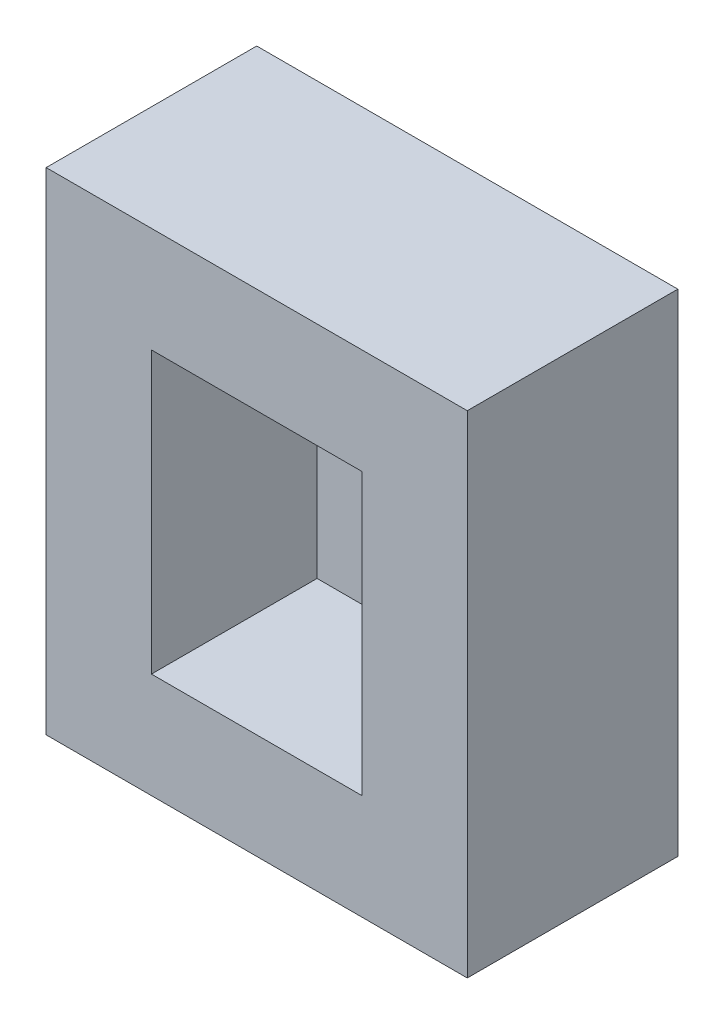
SolidWorks part; units mm, degrees
ref_plane "Front Plane" through (0, 0, 0) normal (0, 0, 1) x (1, 0, 0)
ref_plane "Top Plane" through (0, 0, 0) normal (0, 1, 0) x (1, 0, 0)
ref_plane "Right Plane" through (0, 0, 0) normal (1, 0, 0) x (0, 0, -1)
sketch "Sketch1" plane through (0, 0, 0) normal (0, 1, 0) x (1, 0, 0)
  line L1 (0, 0) -> (609.6, 0)
  line L2 (0, 0) -> (0, 304.8)
  line L3 (0, 304.8) -> (609.6, 304.8)
  line L4 (609.6, 0) -> (609.6, 304.8)
  dimension "D1" = 304.8
  dimension "D2" = 609.6
extrude "Frame" add sketch "Sketch1" along normal blind 711.2 contours L3 L4 L1 L2
sketch "Sketch2" plane through (0, 0, 0) normal (0, 0, 1) x (1, 0, 0)
  line L0 (0, 0) -> (609.6, 0) construction
  line L1 (152.4, 152.4) -> (457.2, 152.4)
  line L2 (152.4, 152.4) -> (152.4, 558.8)
  line L3 (152.4, 558.8) -> (457.2, 558.8)
  line L4 (457.2, 152.4) -> (457.2, 558.8)
  line L5 (0, 711.2) -> (0, 0) construction
  line L6 (0, 711.2) -> (609.6, 711.2) construction
  line L7 (609.6, 711.2) -> (609.6, 0) construction
  dimension "D1" = 152.4
  dimension "D2" = 152.4
  dimension "D3" = 152.4
  dimension "D4" = 152.4
extrude "Space" cut sketch "Sketch2" against normal blind 239.776 contours L2 L1 L4 L3
